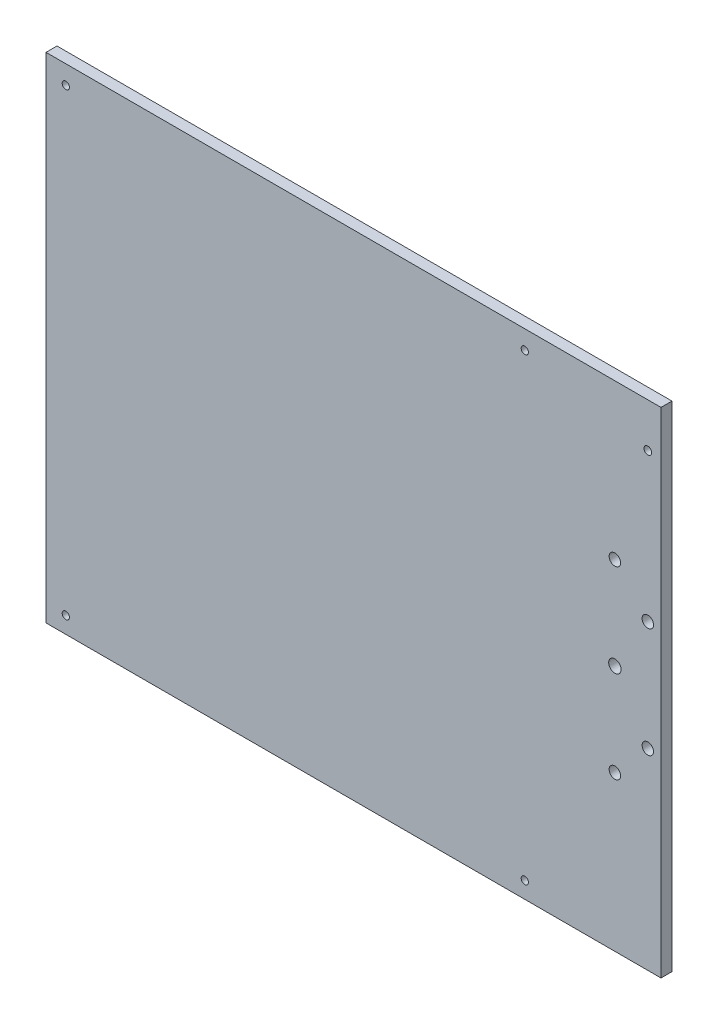
SolidWorks part; units mm, degrees
material "Lega 1060"
ref_plane "Piano frontale" through (0, 0, 0) normal (0, 0, 1) x (1, 0, 0)
ref_plane "Piano superiore" through (0, 0, 0) normal (0, 1, 0) x (1, 0, 0)
ref_plane "Piano destro" through (0, 0, 0) normal (1, 0, 0) x (0, 0, -1)
sketch "Schizzo1" plane through (0, 0, 0) normal (0, 0, 1) x (1, 0, 0)
  line L1 (0, 20) -> (-280, 20)
  line L2 (0, 20) -> (0, 245)
  line L3 (0, 245) -> (-280, 245)
  line L4 (-280, 20) -> (-280, 245)
  dimension "D1" = 280
  dimension "D2" = 225
  dimension "D3" = 20
extrude "Estrusione-Estrusione1" add sketch "Schizzo1" along normal blind 5
hole_wizard "Foro filettato M4-1" positions "Schizzo11" profile "Schizzo10" tap size "M4" standard "ISO" end condition up to next
sketch "Schizzo11" plane through (0, 0, 0) normal (0, 0, -1) x (-1, 0, 0)
  line L0 (280, 20) -> (0, 20) construction
  point P0 (271, 27.5)
  point P2 (62, 27.5)
  point P4 (271, 236.5)
  point P6 (62, 236.5)
  dimension "D1" = 7.5
  dimension "D2" = 209
  dimension "D3" = 209
  dimension "D4" = 9
sketch "Schizzo10" plane through (-271, 27.5, 0) normal (1, 0, 0) x (0, 1, 0)
  line L0 (0, 0) -> (0, 5)
  line L1 (0, 5) -> (1.65, 5)
  line L2 (1.65, 5) -> (1.65, 0)
  line L5 (1.65, 0) -> (0, 0)
  line L11 (0, -6.35) -> (0, 107.95) construction
  dimension "Thru Tap Drill Dia." = 3.3
  dimension "Thru Tap Drill Depth" = 5
cosmetic thread "Filettatura del foro2" parameters "D2"=4
cosmetic thread "Filettatura del foro4" parameters "D2"=4
cosmetic thread "Filettatura del foro5" parameters "D2"=4
cosmetic thread "Filettatura del foro6" parameters "D2"=4
sketch "Schizzo12" plane through (0, 0, 0) normal (0, 0, -1) x (-1, 0, 0)
  line L1 (0, 245) -> (280, 245) construction
  line L2 (6, 107.5) -> (6, 157.5) construction
  line L3 (0, 132.5) -> (280, 132.5) construction
  line L4 (0, 20) -> (0, 245) construction
  line L5 (280, 245) -> (280, 20) construction
  line L6 (21, 132.5) -> (21, 245) construction
  circle A0 centre (6, 107.5) radius 2.6
  circle A1 centre (6, 157.5) radius 2.6
  circle A2 centre (21, 90.5) radius 2.6
  circle A3 centre (21, 132.5) radius 2.8306
  circle A4 centre (21, 174.5) radius 2.6
  circle A5 centre (6, 225) radius 1.75
  dimension "D5" = 3.5
  dimension "D1" = 50
  dimension "D2" = 84
  dimension "D3" = 6
  dimension "D4" = 15
  dimension "D6" = 20
extrude "Taglio-Estrusione1" cut sketch "Schizzo12" against normal blind 10
